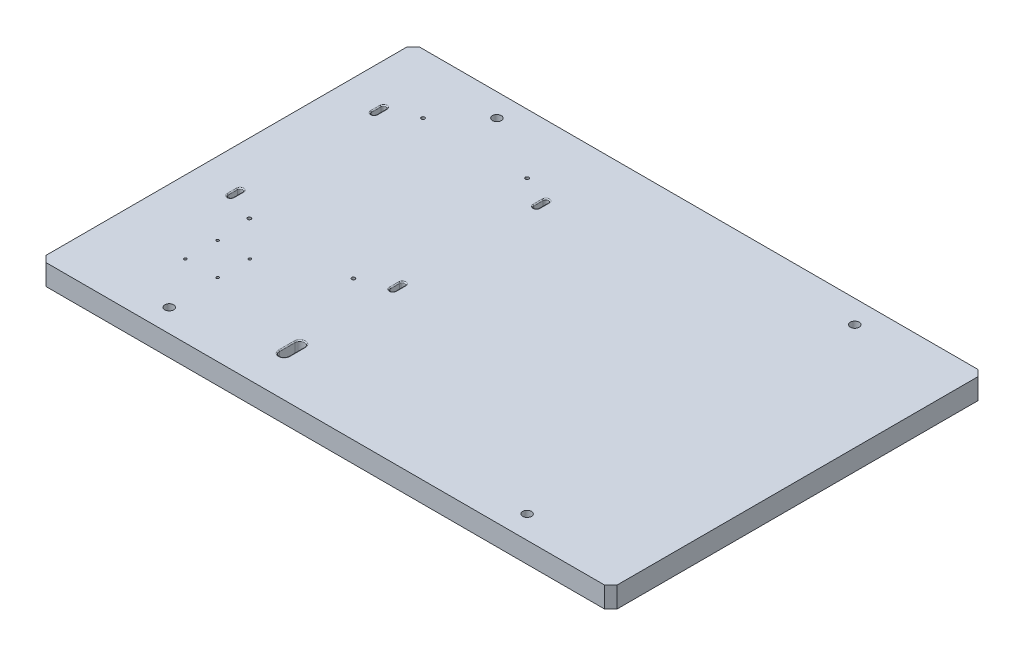
SolidWorks part; units mm, degrees
ref_plane "前视基准面" through (0, 0, 0) normal (0, 0, 1) x (1, 0, 0)
ref_plane "上视基准面" through (0, 0, 0) normal (0, 1, 0) x (1, 0, 0)
ref_plane "右视基准面" through (0, 0, 0) normal (1, 0, 0) x (0, 0, -1)
other "Configuration Table"
sketch "草图1" plane through (0, 0, 0) normal (0, 1, 0) x (1, 0, 0)
  line L0 (214.4987, 34.8483) -> (214.4987, -324.1517) construction
  line L1 (-60.0013, 34.8483) -> (488.9987, 34.8483)
  line L2 (-60.0013, 34.8483) -> (-60.0013, -324.1517)
  line L3 (-60.0013, -324.1517) -> (488.9987, -324.1517)
  line L4 (488.9987, 34.8483) -> (488.9987, -324.1517)
  line L5 (-60.0013, -144.6517) -> (488.9987, -144.6517) construction
  dimension "D1" = 549
  dimension "D2" = 359
extrude "凸台-拉伸1" add sketch "草图1" along normal blind 20
sketch "草图2" plane through (0, 20, 0) normal (0, 1, 0) x (1, 0, 0)
  line L0 (214.4987, 34.8483) -> (214.4987, -324.1517) construction
  line L3 (-60.0013, -144.6517) -> (488.9987, -144.6517) construction
  line L7 (488.9987, 34.8483) -> (-60.0013, 34.8483) construction
  point P5 (42.4987, 12.8483)
  point P21 (386.4987, 12.8483)
  point P22 (42.4987, -302.1517)
  point P23 (386.4987, -302.1517)
  dimension "D1" = 315
  dimension "D2" = 22
  dimension "D3" = 172
hole_wizard "M10 螺纹孔1" positions "草图2" profile "草图3" tap size "M10" standard "GB" end condition through all
sketch "草图3" plane through (386.4987, 20, 302.1517) normal (1, 0, 0) x (0, 0, 1)
  line L0 (0, 0) -> (0, 20)
  line L1 (0, 20) -> (4.25, 20)
  line L2 (4.25, 20) -> (4.25, 0)
  line L5 (4.25, 0) -> (0, 0)
  line L11 (0, -6.35) -> (0, 107.95) construction
  dimension "通孔螺纹孔钻头直径" = 8.5
  dimension "通孔螺纹孔钻头深度" = 20
cosmetic thread "孔螺蚊线1" parameters "D2"=10
cosmetic thread "孔螺蚊线2" parameters "D2"=10
cosmetic thread "孔螺蚊线3" parameters "D2"=10
cosmetic thread "孔螺蚊线4" parameters "D2"=10
sketch "草图4" plane through (0, 20, 0) normal (0, 1, 0) x (1, 0, 0)
  line L0 (-60.0013, -144.6517) -> (488.9987, -144.6517) construction
  line L3 (214.4987, 34.8483) -> (214.4987, -324.1517) construction
  line L6 (-60.0013, -122.6517) -> (-16.0013, -122.6517) construction
  line L7 (-60.0013, 34.8483) -> (-60.0013, -324.1517) construction
  line L8 (-60.0013, -166.6517) -> (-16.0013, -166.6517) construction
  line L9 (-16.0013, -122.6517) -> (-16.0013, -166.6517) construction
  line L10 (488.9987, -166.6517) -> (444.9987, -166.6517) construction
  line L11 (444.9987, -122.6517) -> (444.9987, -166.6517) construction
  line L12 (488.9987, -122.6517) -> (444.9987, -122.6517) construction
  line L13 (192.4987, 34.8483) -> (192.4987, -9.1517) construction
  line L14 (488.9987, 34.8483) -> (-60.0013, 34.8483) construction
  line L15 (236.4987, 34.8483) -> (236.4987, -9.1517) construction
  line L16 (192.4987, -9.1517) -> (236.4987, -9.1517) construction
  line L17 (236.4987, -324.1517) -> (236.4987, -280.1517) construction
  line L18 (192.4987, -280.1517) -> (236.4987, -280.1517) construction
  line L19 (192.4987, -324.1517) -> (192.4987, -280.1517) construction
  line L20 (56.9987, -17.6517) -> (56.9987, -194.6517) construction
  line L21 (-16.0013, -17.6517) -> (129.9987, -17.6517) construction
  line L22 (-16.0013, -17.6517) -> (-16.0013, -194.6517) construction
  line L23 (-16.0013, -194.6517) -> (129.9987, -194.6517) construction
  line L24 (129.9987, -17.6517) -> (129.9987, -194.6517) construction
  line L25 (-16.0013, -106.1517) -> (129.9987, -106.1517) construction
  point P32 (6.9987, -22.6517)
  point P34 (106.9987, -22.6517)
  point P36 (106.9987, -189.6517)
  point P37 (6.9987, -189.6517)
  dimension "D1" = 44
  dimension "D2" = 22
  dimension "D3" = 44
  dimension "D4" = 22
  dimension "D5" = 146
  dimension "D6" = 177
  dimension "D7" = 28
  dimension "D8" = 50
  dimension "D9" = 83.5
hole_wizard "M4 螺纹孔1" positions "草图4" profile "草图5" tap size "M4" standard "GB" end condition through all
sketch "草图5" plane through (6.9987, 20, 189.6517) normal (1, 0, 0) x (0, 0, 1)
  line L0 (0, 0) -> (0, 20)
  line L1 (0, 20) -> (1.65, 20)
  line L2 (1.65, 20) -> (1.65, 0)
  line L5 (1.65, 0) -> (0, 0)
  line L11 (0, -6.35) -> (0, 107.95) construction
  dimension "通孔螺纹孔钻头直径" = 3.3
  dimension "通孔螺纹孔钻头深度" = 20
cosmetic thread "孔螺蚊线5" parameters "D2"=4
cosmetic thread "孔螺蚊线6" parameters "D2"=4
cosmetic thread "孔螺蚊线7" parameters "D2"=4
cosmetic thread "孔螺蚊线8" parameters "D2"=4
sketch "草图9" plane through (0, 20, 0) normal (0, 1, 0) x (1, 0, 0)
  line L0 (-16.0013, -106.1517) -> (129.9987, -106.1517) construction
  line L1 (6.9987, -22.6517) -> (106.9987, -22.6517) construction
  line L2 (6.9987, -22.6517) -> (6.9987, -189.6517) construction
  line L3 (6.9987, -189.6517) -> (106.9987, -189.6517) construction
  line L4 (106.9987, -22.6517) -> (106.9987, -189.6517) construction
  line L5 (-16.0013, -17.6517) -> (129.9987, -17.6517) construction
  line L6 (-16.0013, -17.6517) -> (-16.0013, -194.6517) construction
  line L7 (-16.0013, -194.6517) -> (129.9987, -194.6517) construction
  line L8 (129.9987, -17.6517) -> (129.9987, -194.6517) construction
  line L9 (56.9987, -17.6517) -> (56.9987, -194.6517) construction
  line L10 (-21.0013, -32.6517) -> (-21.0013, -41.6517) construction
  line L11 (-18.5013, -32.6517) -> (-18.5013, -41.6517)
  line L12 (-23.5013, -32.6517) -> (-23.5013, -41.6517)
  line L13 (134.9987, -32.6517) -> (134.9987, -41.6517) construction
  line L14 (132.4987, -32.6517) -> (132.4987, -41.6517)
  line L15 (137.4987, -32.6517) -> (137.4987, -41.6517)
  line L16 (134.9987, -179.6517) -> (134.9987, -170.6517) construction
  line L17 (132.4987, -179.6517) -> (132.4987, -170.6517)
  line L18 (137.4987, -179.6517) -> (137.4987, -170.6517)
  line L19 (-21.0013, -179.6517) -> (-21.0013, -170.6517) construction
  line L20 (-18.5013, -179.6517) -> (-18.5013, -170.6517)
  line L21 (-23.5013, -179.6517) -> (-23.5013, -170.6517)
  line L22 (-60.0013, 34.8483) -> (-60.0013, -324.1517) construction
  line L23 (-60.0013, -122.6517) -> (-16.0013, -122.6517) construction
  line L24 (-60.0013, -144.6517) -> (488.9987, -144.6517) construction
  line L25 (-60.0013, -166.6517) -> (-16.0013, -166.6517) construction
  line L26 (214.4987, 34.8483) -> (214.4987, -324.1517) construction
  line L27 (-16.0013, -122.6517) -> (-16.0013, -166.6517) construction
  line L28 (488.9987, -122.6517) -> (444.9987, -122.6517) construction
  line L29 (488.9987, -166.6517) -> (444.9987, -166.6517) construction
  line L30 (444.9987, -122.6517) -> (444.9987, -166.6517) construction
  line L31 (192.4987, 34.8483) -> (192.4987, -9.1517) construction
  line L32 (488.9987, 34.8483) -> (-60.0013, 34.8483) construction
  line L33 (236.4987, 34.8483) -> (236.4987, -9.1517) construction
  line L34 (192.4987, -9.1517) -> (236.4987, -9.1517) construction
  line L35 (236.4987, -324.1517) -> (236.4987, -280.1517) construction
  line L36 (192.4987, -324.1517) -> (192.4987, -280.1517) construction
  line L37 (192.4987, -280.1517) -> (236.4987, -280.1517) construction
  arc A0 (-18.5013, -32.6517) -> (-23.5013, -32.6517) centre (-21.0013, -32.6517) ccw
  arc A1 (-23.5013, -41.6517) -> (-18.5013, -41.6517) centre (-21.0013, -41.6517) ccw
  arc A2 (132.4987, -32.6517) -> (137.4987, -32.6517) centre (134.9987, -32.6517) cw
  arc A3 (137.4987, -41.6517) -> (132.4987, -41.6517) centre (134.9987, -41.6517) cw
  arc A4 (132.4987, -179.6517) -> (137.4987, -179.6517) centre (134.9987, -179.6517) ccw
  arc A5 (137.4987, -170.6517) -> (132.4987, -170.6517) centre (134.9987, -170.6517) ccw
  arc A6 (-18.5013, -179.6517) -> (-23.5013, -179.6517) centre (-21.0013, -179.6517) cw
  arc A7 (-23.5013, -170.6517) -> (-18.5013, -170.6517) centre (-21.0013, -170.6517) cw
  point P15 (-21.0013, -37.1517)
  point P23 (134.9987, -37.1517)
  point P30 (134.9987, -175.1517)
  point P37 (-21.0013, -175.1517)
  dimension "D1" = 146
  dimension "D2" = 177
  dimension "D3" = 23
  dimension "D4" = 5
  dimension "D5" = 9
  dimension "D6" = 5
  dimension "D7" = 15
  dimension "D8" = 2.5
  dimension "D9" = 22
  dimension "D10" = 44
  dimension "D11" = 22
  dimension "D12" = 315
  dimension "D13" = 271
  dimension "D14" = 208.5
extrude "切除-拉伸1" cut sketch "草图9" against normal through all and the other way through all
chamfer "倒角1" distance 6 angle 45 4 edges at (-60.0013, 10, 324.1517) (488.9987, 10, 324.1517) (488.9987, 10, -34.8483) (-60.0013, 10, -34.8483)
fillet "圆角2" radius 1 32 edges at (-23.5013, 0, 37.1517) (-21.0013, 0, 30.1517) (-18.5013, 0, 37.1517) (-23.5013, 20, 37.1517) (-21.0013, 20, 30.1517) (-18.5013, 20, 37.1517) (132.4987, 0, 37.1517) (134.9987, 0, 30.1517) (137.4987, 0, 37.1517) (132.4987, 20, 37.1517) (134.9987, 20, 30.1517) (137.4987, 20, 37.1517) (132.4987, 0, 175.1517) (134.9987, 0, 168.1517) (137.4987, 0, 175.1517) (132.4987, 20, 175.1517) (134.9987, 20, 168.1517) (137.4987, 20, 175.1517) (-23.5013, 0, 175.1517) (-21.0013, 0, 168.1517) (-18.5013, 0, 175.1517) (-23.5013, 20, 175.1517) (-21.0013, 20, 168.1517) (-18.5013, 20, 175.1517) (-21.0013, 0, 44.1517) (-21.0013, 20, 44.1517) (134.9987, 0, 44.1517) (134.9987, 20, 44.1517) (134.9987, 0, 182.1517) (134.9987, 20, 182.1517) (-21.0013, 0, 182.1517) (-21.0013, 20, 182.1517)
sketch "草图16" plane through (0, 0, 0) normal (0, -1, 0) x (1, 0, 0)
  line L0 (-60.0013, -28.8483) -> (-60.0013, 318.1517) construction
  line L2 (135.9987, 270.1829) -> (135.9987, 285.1829) construction
  line L4 (131.4987, 270.1829) -> (131.4987, 285.1829)
  line L5 (140.4987, 270.1829) -> (140.4987, 285.1829)
  arc A0 (131.4987, 270.1829) -> (140.4987, 270.1829) centre (135.9987, 270.1829) ccw
  arc A1 (140.4987, 285.1829) -> (131.4987, 285.1829) centre (135.9987, 285.1829) ccw
  point P4 (135.9987, 277.6829)
  dimension "D7" = 196
  dimension "D5" = 15
  dimension "D6" = 9
extrude "切除-拉伸4" cut sketch "草图16" along direction (0, 1, 0) on the side against the normal up to surface (20 mm away)
sketch "草图18" plane through (0, 0, 0) normal (0, -1, 0) x (1, 0, 0)
  line L0 (-60.0013, -28.8483) -> (-60.0013, 318.1517) construction
  line L1 (-54.0013, 324.1517) -> (482.9987, 324.1517) construction
  point P0 (9.9987, 254.1517)
  point P1 (40.9987, 254.1517)
  point P2 (9.9987, 223.1517)
  point P3 (40.9987, 223.1517)
  dimension "D1" = 31
  dimension "D2" = 31
  dimension "D3" = 70
  dimension "D4" = 70
hole_wizard "M3 螺纹孔2" positions "草图18" profile "草图19" tap size "M3" standard "GB" end condition up to next
sketch "草图19" plane through (9.9987, 0, 254.1517) normal (1, 0, 0) x (0, 0, -1)
  line L0 (0, 0) -> (0, 20)
  line L1 (0, 20) -> (1.25, 20)
  line L2 (1.25, 20) -> (1.25, 0)
  line L5 (1.25, 0) -> (0, 0)
  line L11 (0, -6.35) -> (0, 107.95) construction
  dimension "通孔螺纹孔钻头直径" = 2.5
  dimension "通孔螺纹孔钻头深度" = 20
cosmetic thread "孔螺蚊线13" parameters "D2"=3
cosmetic thread "孔螺蚊线14" parameters "D2"=3
cosmetic thread "孔螺蚊线15" parameters "D2"=3
cosmetic thread "孔螺蚊线16" parameters "D2"=3
fillet "圆角4" radius 1 8 edges at (140.4987, 20, 277.6829) (135.9987, 20, 265.6829) (131.4987, 20, 277.6829) (140.4987, 0, 277.6829) (135.9987, 0, 265.6829) (131.4987, 0, 277.6829) (135.9987, 20, 289.6829) (135.9987, 0, 289.6829)
sketch "草图20" plane through (0, 0, 0) normal (0, -1, 0) x (1, 0, 0)
  circle A0 centre (42.4987, 302.1517) radius 8.1
  circle A1 centre (386.4987, 302.1517) radius 8.1
  circle A2 centre (386.4987, -12.8483) radius 8.1
  circle A3 centre (42.4987, -12.8483) radius 8.1
  dimension "D1" = 16.2
  dimension "D2" = 16.2
  dimension "D3" = 16.2
  dimension "D4" = 16.2
extrude "切除-拉伸5" cut sketch "草图20" against normal blind 10
